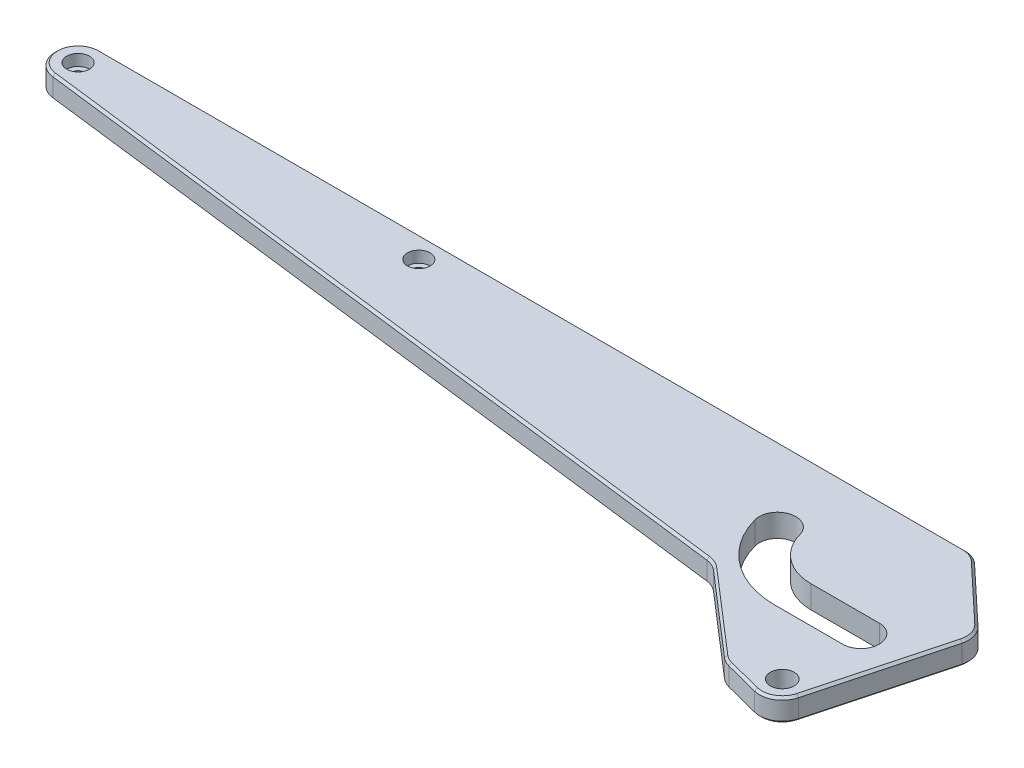
SolidWorks part; units mm, degrees
ref_plane "Front Plane" through (0, 0, 0) normal (0, 0, 1) x (1, 0, 0)
ref_plane "Top Plane" through (0, 0, 0) normal (0, 1, 0) x (1, 0, 0)
ref_plane "Right Plane" through (0, 0, 0) normal (1, 0, 0) x (0, 0, -1)
sketch "Sketch1" plane through (0, 0, 0) normal (0, 1, 0) x (1, 0, 0)
  line L3 (-390, 90) -> (34.4682, 90)
  line L4 (-391.2187, 70.0745) -> (-60, 29.406)
  line L5 (9.6593, -2.5882) -> (34.4682, 90)
  line L6 (-2.499, -9.6827) -> (-20, -5.1659)
  line L7 (-20, -5.1659) -> (-60, 29.406)
  arc A2 (-2.499, -9.6827) -> (9.6593, -2.5882) centre (0, 0) ccw
  arc A3 (-390, 90) -> (-391.2187, 70.0745) centre (-390, 80) ccw
  dimension "D1" = 20
  dimension "D2" = 390
  dimension "D3" = 80
  dimension "D4" = 7
  dimension "D5" = 75
  dimension "D6" = 20
  dimension "D7" = 40
extrude "Boss-Extrude1" add sketch "Sketch1" along normal mid plane 10
sketch "Slot Path" plane through (0, 0, 0) normal (0, 1, 0) x (1, 0, 0)
  line L0 (-30, 34.641) -> (0, 34.641)
  line L1 (0, -5.5) -> (0, 5.5) construction
  line L2 (-5.5, 0) -> (5.5, 0) construction
  arc A0 (-30, 34.641) -> (-58.9778, 56.8764) centre (-30, 64.641) cw
  dimension "D1" = 30
  dimension "D2" = 34.641
sketch "Sketch4" plane through (0, 5, 0) normal (0, 1, 0) x (1, 0, 0)
  line L30 (-30, 26.591) -> (0, 26.591)
  line L31 (-30, 42.691) -> (0, 42.691)
  arc A52 (-66.7535, 54.793) -> (-30, 26.591) centre (-30, 64.641) ccw
  arc A53 (-51.2021, 58.9599) -> (-30, 42.691) centre (-30, 64.641) ccw
  arc A54 (-66.7535, 54.793) -> (-51.2021, 58.9599) centre (-58.9778, 56.8764) cw
  arc A55 (0, 26.591) -> (0, 42.691) centre (0, 34.641) ccw
extrude "Slot" cut sketch "Sketch4" against normal through all
hole_wizard "Ø10.5 (10.5) Diameter Hole1" positions "Sketch9" profile "Sketch10" hole size "Ø10.5" standard "ANSI Metric"
sketch "Sketch9" plane through (0, 5, 0) normal (0, 1, 0) x (1, 0, 0)
  point P0 (0, 0)
sketch "Sketch10" plane through (0, 5, 0) normal (1, 0, 0) x (0, 0, 1)
  line L0 (0, 0) -> (0, 18.1545)
  line L1 (0, 18.1545) -> (5.25, 15)
  line L2 (5.25, 15) -> (5.25, 0)
  line L5 (5.25, 0) -> (0, 0)
  line L10 (0, 18.1545) -> (-5.25, 15) construction
  line L11 (0, -6.35) -> (0, 107.95) construction
  dimension "Hole Dia." = 10.5
  dimension "Hole Depth" = 15
  dimension "Drill Angle" = 118
hole_wizard "CBORE for M5 SHCS1" positions "Sketch11" profile "Sketch12" counterbore size "M5" standard "ANSI Metric"
sketch "Sketch11" plane through (0, 5, 0) normal (0, 1, 0) x (1, 0, 0)
  arc A0 (-390, 90) -> (-391.2187, 70.0745) centre (-390, 80) ccw construction
  point P0 (-390, 80)
  point P2 (-240, 80)
  dimension "D1" = 150
sketch "Sketch12" plane through (-390, 5, -80) normal (1, 0, 0) x (0, 0, 1)
  line L0 (0, 0) -> (0, 16.6524)
  line L1 (0, 16.6524) -> (2.75, 15)
  line L2 (2.75, 15) -> (2.75, 5)
  line L3 (2.75, 5) -> (5, 5)
  line L4 (5, 5) -> (5, 0)
  line L5 (5, 0) -> (0, 0)
  line L10 (0, 16.6524) -> (-2.75, 15) construction
  line L11 (0, -6.35) -> (0, 107.95) construction
  dimension "Hole Dia." = 5.5
  dimension "Hole Depth" = 15
  dimension "C'Bore Dia." = 10
  dimension "C'Bore Depth" = 5
  dimension "Drill Angle" = 118
sketch "Sketch13" plane through (0, 5, 0) normal (0, 1, 0) x (1, 0, 0)
  line L0 (-5.5318, 90) -> (34.4682, 90)
  line L1 (34.4682, 90) -> (-390, 90) construction
  line L2 (9.6593, -2.5882) -> (34.4682, 90) construction
  line L3 (34.4682, 90) -> (26.4297, 60)
  line L4 (26.4297, 60) -> (-5.5318, 90)
  dimension "D1" = 30
  dimension "D2" = 40
extrude "Cut-Extrude3" cut sketch "Sketch13" against normal through all
fillet "Fillet1" radius 10 4 edges at (-5.5318, 0, -90) (26.4297, 0, -60) (-20, 0, 5.1659) (-60, 0, -29.406)
chamfer "Chamfer1" distance 1 angle 45 24 edges at (-10.1155, -5, 7.717) (-19.8744, -5, 4.9261) (-39.7354, -5, -11.8914) (-60.1834, -5, -28.9925) (-227.1189, -5, -49.9256) (-399.9813, -5, -80.6105) (-199.7449, -5, -90) (-5.8096, -5, -89.2982) (9.7094, -5, -75.6941) (24.8381, -5, -59.5464) (17.2698, -5, -25.8147) (5.0399, -5, 8.6371) (-399.9813, 5, -80.6105) (-227.1189, 5, -49.9256) (-60.1834, 5, -28.9925) (-39.7354, 5, -11.8914) (-19.8744, 5, 4.9261) (-10.1155, 5, 7.717) (5.0399, 5, 8.6371) (17.2698, 5, -25.8147) (24.8381, 5, -59.5464) (9.7094, 5, -75.6941) (-5.8096, 5, -89.2982) (-199.7449, 5, -90)
